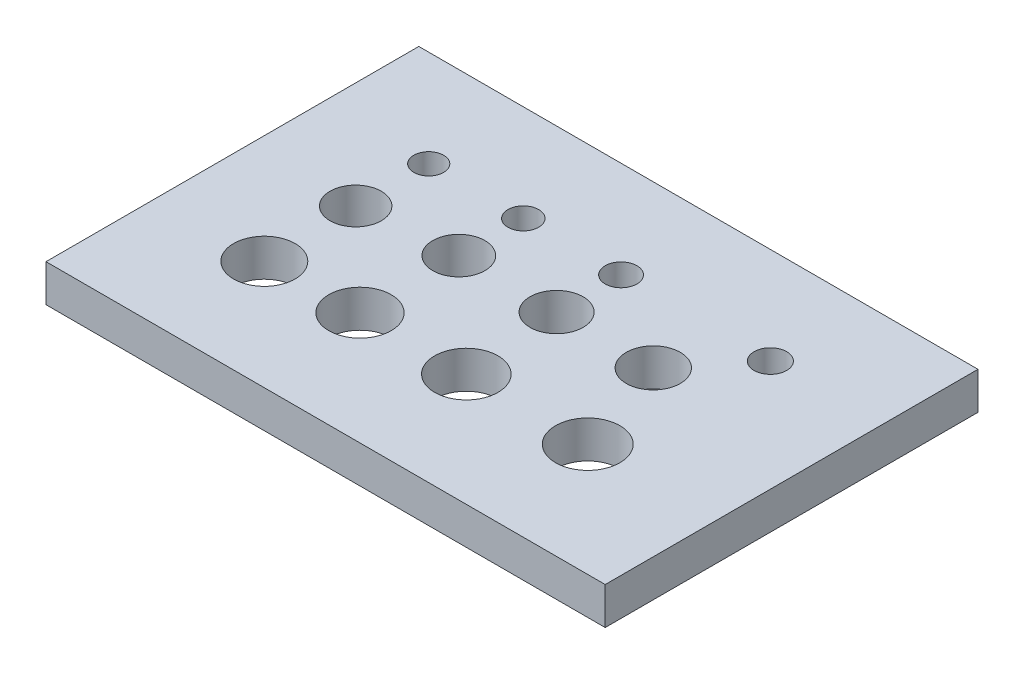
SolidWorks part; units mm, degrees
ref_plane "前视基准面" through (0, 0, 0) normal (0, 0, 1) x (1, 0, 0)
ref_plane "上视基准面" through (0, 0, 0) normal (0, 1, 0) x (1, 0, 0)
ref_plane "右视基准面" through (0, 0, 0) normal (1, 0, 0) x (0, 0, -1)
other "Configuration Table"
sketch "草图1" plane through (0, 0, 0) normal (0, 1, 0) x (1, 0, 0)
  line L1 (-15, 10) -> (15, 10)
  line L2 (-15, 10) -> (-15, -10)
  line L3 (-15, -10) -> (15, -10)
  line L4 (15, 10) -> (15, -10)
  line L5 (-15, 10) -> (15, -10) construction
  line L6 (-15, -10) -> (15, 10) construction
  circle A0 centre (-9.2795, 4.8127) radius 0.8
  circle A1 centre (-4.2075, 4.8127) radius 0.825
  circle A2 centre (1.0375, 4.8127) radius 0.85
  circle A3 centre (9.049, 4.8127) radius 0.875
  circle A4 centre (-9.2795, 0.8934) radius 1.375
  circle A5 centre (-4.2075, 1.3545) radius 1.4
  circle A6 centre (1.0375, 1.3545) radius 1.425
  circle A7 centre (6.2248, 1.3545) radius 1.45
  circle A8 centre (-9.1618, -4.1248) radius 1.65
  circle A9 centre (-4.2075, -3.9481) radius 1.675
  circle A10 centre (1.4986, -3.9481) radius 1.7
  circle A11 centre (8.0115, -3.9481) radius 1.725
  point P0 (0, 0)
  dimension "D3" = 1.6
  dimension "D4" = 1.65
  dimension "D5" = 1.7
  dimension "D6" = 1.75
  dimension "D7" = 2.75
  dimension "D8" = 2.8
  dimension "D9" = 2.85
  dimension "D10" = 2.9
  dimension "D11" = 3.3
  dimension "D12" = 3.35
  dimension "D13" = 3.4
  dimension "D14" = 3.45
  dimension "D1" = 20
  dimension "D2" = 30
extrude "凸台-拉伸1" add sketch "草图1" along normal blind 2
